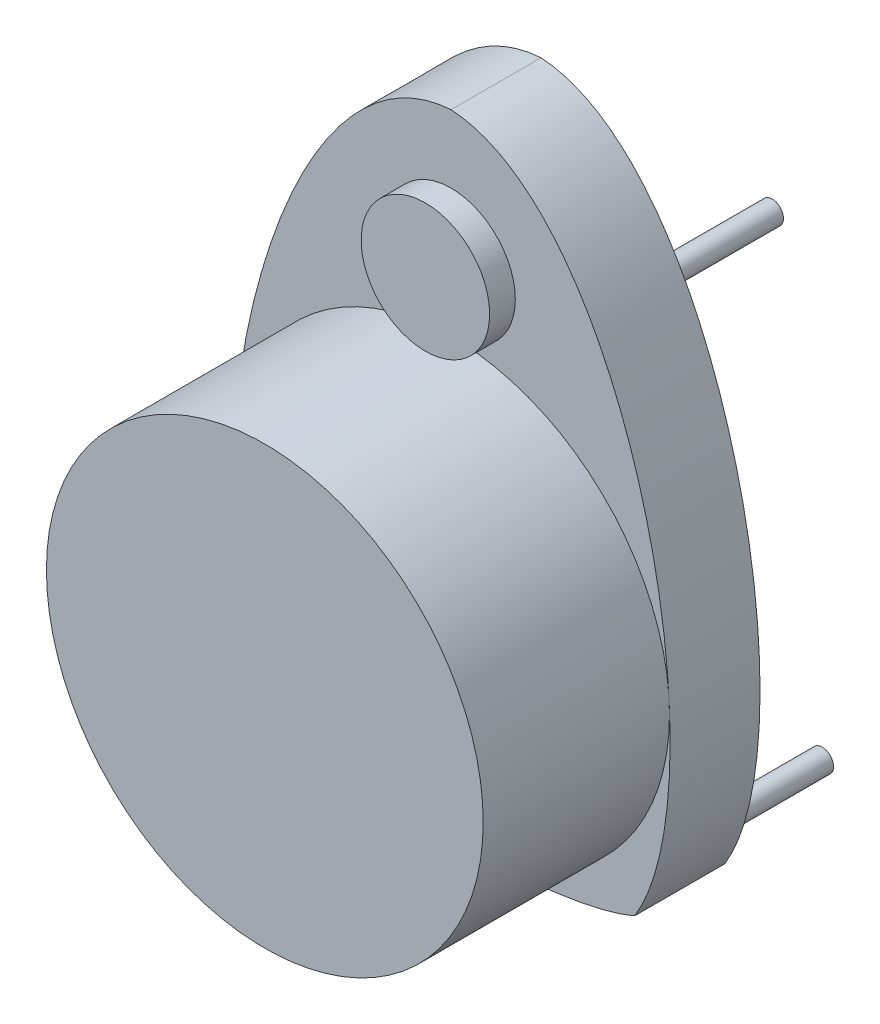
SolidWorks part; units mm, degrees
ref_plane "前基準面" through (0, 0, 0) normal (0, 0, 1) x (1, 0, 0)
ref_plane "上基準面" through (0, 0, 0) normal (0, 1, 0) x (1, 0, 0)
ref_plane "右基準面" through (0, 0, 0) normal (1, 0, 0) x (0, 0, -1)
sketch "草圖1" plane through (0, 0, 0) normal (0, 0, 1) x (1, 0, 0)
  circle A0 centre (0, 0) radius 34
  dimension "D1" = 68
sketch "草圖4" plane through (0, 0, 0) normal (0, 0, 1) x (1, 0, 0)
  line L0 (0, 0) -> (0, 44) construction
  circle A0 centre (0, 44) radius 10
  dimension "D2" = 20
  dimension "D1" = 44
extrude "填料-伸長2" add sketch "草圖1" along normal blind 29 contours A0
extrude "填料-伸長3" add sketch "草圖4" along normal blind 4 separate body contours A0
sketch "草圖5" plane through (0, 0, 0) normal (0, 0, 1) x (1, 0, 0)
  line L0 (0, 44) -> (0, 63) construction
  circle A0 centre (0, 0) radius 34 construction
  spline S0 degree 3 poles (0, 64.569) (-28.2258, 62.7668) (-42.774, -6.4129) (-28.6113, -29.8037) knots 0 0 0 0 1 1 1 1
  spline S1 degree 3 poles (0, 64.569) (28.2258, 62.7668) (42.774, -6.4129) (28.6113, -29.8037) knots 0 0 0 0 1 1 1 1
  spline S2 degree 2 poles (-28.6113, -29.8037) (-20.2773, -33.5077) (0, -34) knots 0 0 0 1 1 1
  spline S3 degree 2 poles (28.6113, -29.8037) (20.2773, -33.5077) (0, -34) knots 0 0 0 1 1 1
  dimension "D1" = 19
extrude "填料-伸長5" add sketch "草圖5" against normal blind 14 separate body
sketch "草圖6" plane through (0, 0, -14) normal (0, 0, -1) x (-1, 0, 0)
  line L0 (0, 64.569) -> (0, 45.769) construction
  line L1 (20, 45.769) -> (-20, 45.769) construction
  line L2 (0, 45.769) -> (0, -24.231) construction
  line L3 (27.8, -24.231) -> (-27.8, -24.231) construction
  circle A0 centre (-27.8, -24.231) radius 1.75
  circle A1 centre (27.8, -24.231) radius 1.75
  circle A2 centre (-20, 45.769) radius 1.75
  circle A3 centre (20, 45.769) radius 1.75
  dimension "D5" = 3.5
  dimension "D6" = 2
  dimension "D7" = 3.5
  dimension "D8" = 3.5
  dimension "D1" = 18.8
  dimension "D2" = 20
  dimension "D3" = 70
  dimension "D4" = 27.8
extrude "填料-伸長6" add sketch "草圖6" along normal blind 16
